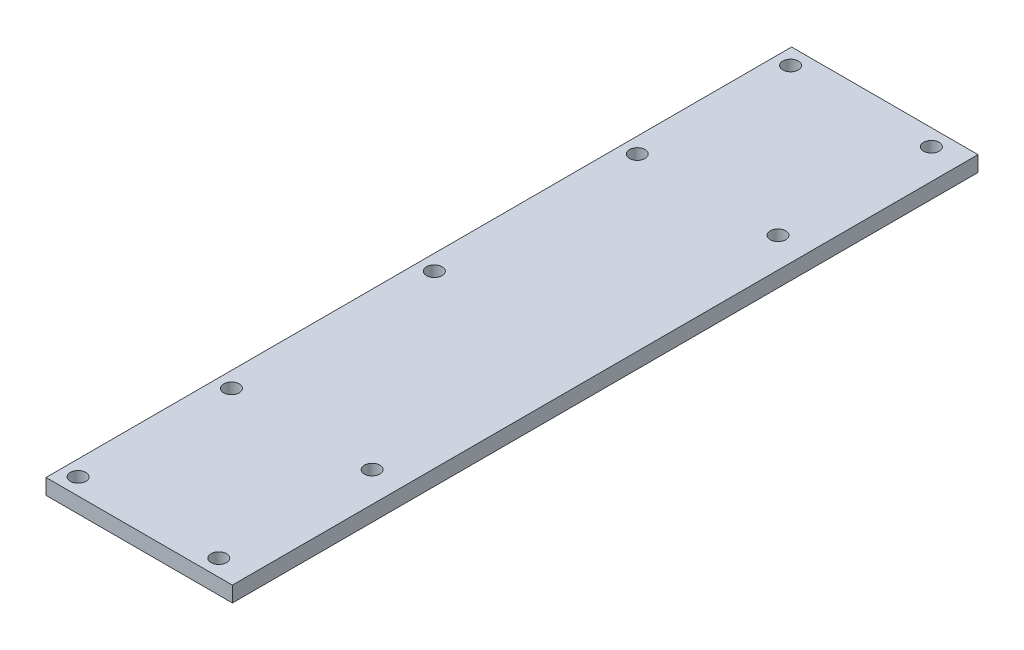
SolidWorks part; units mm, degrees
ref_plane "Front Plane" through (0, 0, 0) normal (0, 0, 1) x (1, 0, 0)
ref_plane "Top Plane" through (0, 0, 0) normal (0, 1, 0) x (1, 0, 0)
ref_plane "Right Plane" through (0, 0, 0) normal (1, 0, 0) x (0, 0, -1)
sketch "Sketch1" plane through (0, 0, 0) normal (0, 1, 0) x (1, 0, 0)
  line L1 (-85.3722, 92.075) -> (67.0278, 92.075)
  line L2 (-85.3722, 92.075) -> (-85.3722, -517.525)
  line L3 (-85.3722, -517.525) -> (67.0278, -517.525)
  line L4 (67.0278, 92.075) -> (67.0278, -517.525)
  dimension "D1" = 152.4
  dimension "D2" = 609.6
extrude "Boss-Extrude1" add sketch "Sketch1" along normal blind 12.7
sketch "Sketch2" plane through (0, 12.7, 0) normal (0, 1, 0) x (1, 0, 0)
  line L0 (-72.6722, -390.525) -> (-72.6722, -34.925) construction
  line L1 (-669.5722, -390.525) -> (-59.9722, -390.525) construction
  line L2 (-59.9722, -34.925) -> (-669.5722, -34.925) construction
  line L3 (-85.3722, -212.725) -> (-59.9722, -212.725) construction
  line L4 (-85.3722, 92.075) -> (-85.3722, -517.525) construction
  line L5 (-59.9722, -390.525) -> (-59.9722, -34.925) construction
  line L6 (-9.1722, -517.525) -> (-9.1722, 92.075) construction
  line L7 (-85.3722, -517.525) -> (67.0278, -517.525) construction
  line L8 (67.0278, 92.075) -> (-85.3722, 92.075) construction
  line L9 (-85.3722, -212.725) -> (67.0278, -212.725) construction
  line L10 (67.0278, -517.525) -> (67.0278, 92.075) construction
  line L11 (-161.7196, -504.0107) -> (16.3751, -504.0107) construction
  line L12 (-110.9196, -378.6393) -> (87.4137, -378.6393) construction
  line L13 (-364.7722, -390.525) -> (-364.7722, -34.925) construction
  circle A0 centre (-72.6722, -212.725) radius 6.35
  circle A1 centre (-72.6722, -378.6393) radius 6.35
  circle A2 centre (-72.6722, -504.0107) radius 6.35
  circle A3 centre (42.3866, -504.0107) radius 6.35
  circle A4 centre (42.3866, -378.6393) radius 6.35
  circle A5 centre (42.3866, -46.8107) radius 6.35
  circle A6 centre (42.3866, 78.5607) radius 6.35
  circle A7 centre (-72.6722, -46.8107) radius 6.35
  circle A8 centre (-72.6722, 78.5607) radius 6.35
  point P14 (-72.6722, -212.725)
  dimension "D1" = 12.7
  dimension "D2" = 12.7
  dimension "D3" = 63.5
  dimension "D4" = 51.5588
extrude "Cut-Extrude1" cut sketch "Sketch2" against normal blind 12.7
